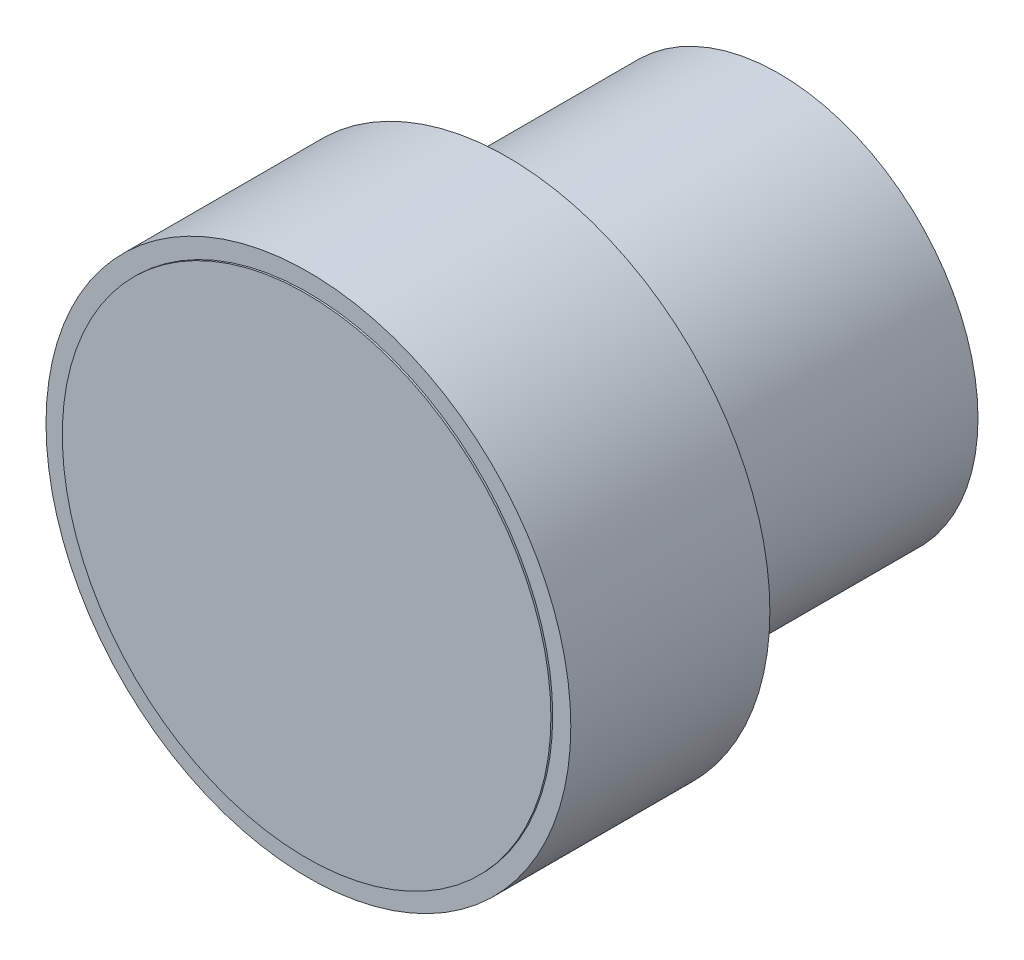
SolidWorks part; units mm, degrees
ref_plane "前视基准面" through (0, 0, 0) normal (0, 0, 1) x (1, 0, 0)
ref_plane "上视基准面" through (0, 0, 0) normal (0, 1, 0) x (1, 0, 0)
ref_plane "右视基准面" through (0, 0, 0) normal (1, 0, 0) x (0, 0, -1)
sketch "草图1" plane through (0, 0, 0) normal (0, 0, 1) x (1, 0, 0)
  circle A0 centre (0, 0) radius 11
extrude "凸台-拉伸1" add sketch "草图1" along normal blind 15
sketch "草图2" plane through (0, 0, 15) normal (0, 0, 1) x (1, 0, 0)
  circle A0 centre (0, 0) radius 14.5
extrude "凸台-拉伸2" add sketch "草图2" along normal blind 11
sketch "草图3" plane through (0, 0, 26) normal (0, 0, 1) x (1, 0, 0)
  circle A1 centre (0, 0) radius 13.5
  point P0 (0, 0)
extrude "凸台-拉伸3" add sketch "草图3" along normal blind 0.1
